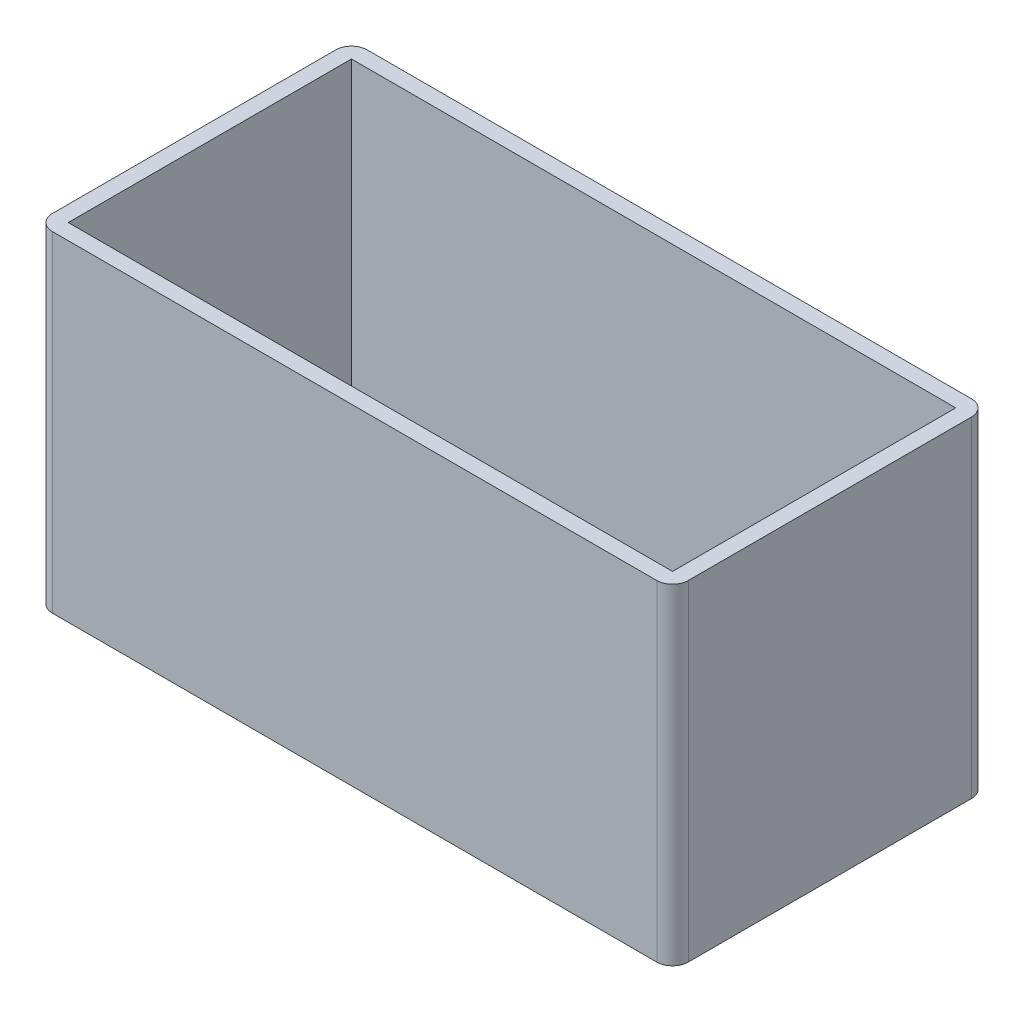
SolidWorks part; units mm, degrees
material "ABS"
ref_plane "Plan de face" through (0, 0, 0) normal (0, 0, 1) x (1, 0, 0)
ref_plane "Plan de dessus" through (0, 0, 0) normal (0, 1, 0) x (1, 0, 0)
ref_plane "Plan de droite" through (0, 0, 0) normal (1, 0, 0) x (0, 0, -1)
sketch "Esquisse1" plane through (0, 0, 0) normal (0, 1, 0) x (1, 0, 0)
  line L0 (-37.6238, 0) -> (35.0495, 0) construction
  line L1 (0, 28.6139) -> (0, -20.297) construction
  line L2 (-27.9109, 9) -> (10.4891, 9)
  line L3 (-28.9109, 10) -> (11.4891, 10)
  line L4 (-28.9109, 10) -> (-28.9109, -10)
  line L5 (-28.9109, -10) -> (11.4891, -10)
  line L6 (11.4891, 10) -> (11.4891, -10)
  line L7 (10.4891, 9) -> (10.4891, -9)
  line L8 (-27.9109, -9) -> (10.4891, -9)
  line L9 (-27.9109, 9) -> (-27.9109, -9)
  dimension "D1" = 20
  dimension "D2" = 40.4
  dimension "D3" = 1
extrude "Boss.-Extru.1" add sketch "Esquisse1" along normal blind 21
fillet "Congé1" radius 1 4 edges at (-28.9109, 10.5, -10) (-28.9109, 10.5, 10) (11.4891, 10.5, -10) (11.4891, 10.5, 10)
